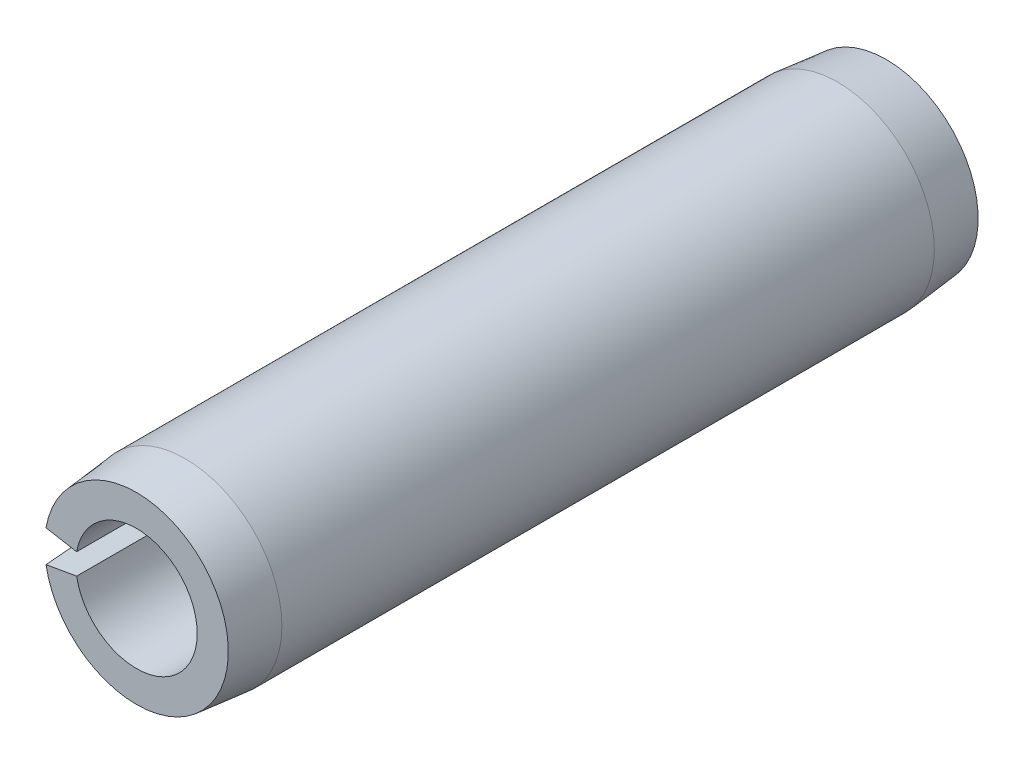
SolidWorks part; units mm, degrees
material "AISI 304"
ref_plane "Front Plane" through (0, 0, 0) normal (0, 0, 1) x (1, 0, 0)
ref_plane "Top Plane" through (0, 0, 0) normal (0, 1, 0) x (1, 0, 0)
ref_plane "Right Plane" through (0, 0, 0) normal (1, 0, 0) x (0, 0, -1)
sketch "Sketch1" plane through (0, 0, 0) normal (0, 0, 1) x (1, 0, 0)
  line L0 (2.0574, 0) -> (3.2766, 0) construction
  line L1 (-3.2268, 0.569) -> (-2.0261, 0.3573)
  line L2 (-2.0261, -0.3573) -> (-3.2268, -0.569)
  arc A0 (-3.2268, -0.569) -> (-3.2268, 0.569) centre (0, 0) ccw
  arc A1 (-2.0261, -0.3573) -> (-2.0261, 0.3573) centre (0, 0) ccw
  dimension "OD" = 6.5532
  dimension "Wall thickness" = 1.2192
  dimension "D3" = 20
extrude "Extrude1" add sketch "Sketch1" along normal mid plane 25.4
sketch "Sketch2" plane through (0, 0, 0) normal (1, 0, 0) x (0, 0, -1)
  line L0 (0, -3.2766) -> (0, 3.2766) construction
  line L1 (12.7, 0) -> (-12.7, 0) construction
  line L2 (12.7, -2.0574) -> (12.7, 2.0574) construction
  line L3 (12.7, 3.2766) -> (-12.7, 3.2766) construction
  line L4 (12.7, 3.2766) -> (12.7, 3.1115)
  line L5 (12.7, 3.1115) -> (11.049, 3.2766)
  line L6 (11.049, 3.2766) -> (12.7, 3.2766)
  line L7 (12.7, -3.2766) -> (12.7, 3.2766) construction
  line L8 (-11.049, 3.2766) -> (-12.7, 3.2766)
  line L9 (-12.7, 3.1115) -> (-11.049, 3.2766)
  line L10 (-12.7, 3.2766) -> (-12.7, 3.1115)
  line L11 (11.049, -3.2766) -> (12.7, -3.2766) construction
  line L12 (12.7, -3.1115) -> (11.049, -3.2766) construction
  line L13 (12.7, -3.2766) -> (12.7, -3.1115) construction
  dimension "B" = 6.223
  dimension "Chamfer max" = 1.651
revolve "Cut-Revolve1" cut sketch "Sketch2" angle 360 about L1
sketch "Sketch3" plane through (0, 0, 0) normal (0, 0, 1) x (1, 0, 0)
  line L0 (2.0574, 0) -> (3.2766, 0) construction
  line L1 (2.0574, 0) -> (3.2766, 0)
  circle A0 centre (0, 0) radius 3.2766
  circle A1 centre (0, 0) radius 2.0574
  arc A2 (-3.2268, -0.569) -> (-3.2268, 0.569) centre (0, 0) ccw construction
  arc A3 (-2.0261, -0.3573) -> (-2.0261, 0.3573) centre (0, 0) ccw construction
